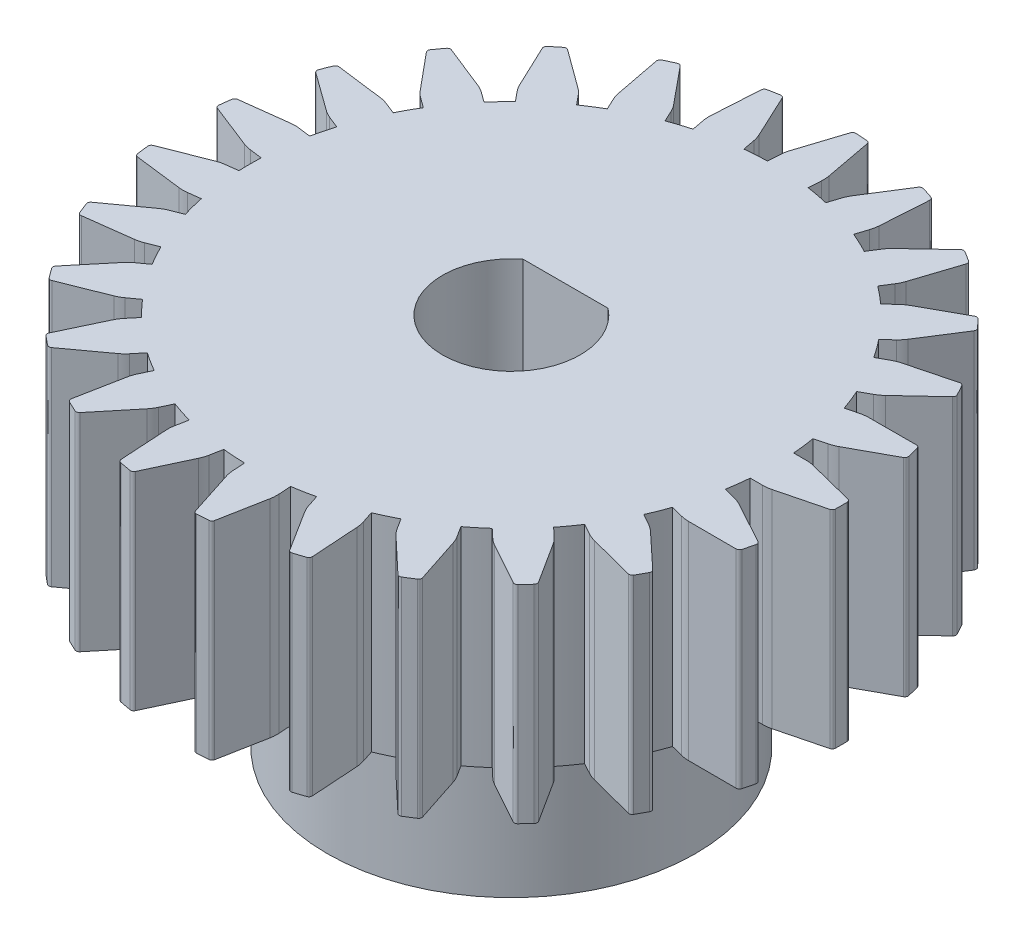
SolidWorks part; units mm, degrees
ref_plane "Front Plane" through (0, 0, 0) normal (0, 0, 1) x (1, 0, 0)
ref_plane "Top Plane" through (0, 0, 0) normal (0, 1, 0) x (1, 0, 0)
ref_plane "Right Plane" through (0, 0, 0) normal (1, 0, 0) x (0, 0, -1)
sketch "Sketch1" plane through (0, 0, 0) normal (0, 1, 0) x (1, 0, 0)
  line L0 (2.0888, 4.0389) -> (-2.9918, 4.0389)
  line L1 (-19.9606, 2.7118) -> (-17.3123, 1.6707)
  line L2 (-16.8313, 1.5479) -> (-16.0874, 1.4539)
  line L3 (-16.0874, 0.124) -> (-16.8313, 0.03)
  line L4 (-17.3123, -0.0928) -> (-19.9606, -1.1339)
  line L5 (-19.8259, -2.2003) -> (-17.0019, -2.5501)
  line L6 (-16.5054, -2.5495) -> (-15.7615, -2.4555)
  line L7 (-15.4308, -3.7436) -> (-16.128, -4.0196)
  line L8 (-16.5633, -4.2583) -> (-18.8695, -5.9252)
  line L9 (-18.4738, -6.9246) -> (-15.6516, -6.5611)
  line L10 (-15.1708, -6.437) -> (-14.4737, -6.161)
  line L11 (-13.833, -7.3264) -> (-14.4396, -7.7671)
  line L12 (-14.802, -8.1065) -> (-16.6211, -10.2946)
  line L13 (-15.9893, -11.1643) -> (-13.3461, -10.1103)
  line L14 (-12.9114, -9.8706) -> (-12.3048, -9.4298)
  line L15 (-11.3944, -10.3993) -> (-11.8724, -10.977)
  line L16 (-12.1389, -11.3959) -> (-13.3568, -13.9676)
  line L17 (-12.5285, -14.6528) -> (-10.2305, -12.9746)
  line L18 (-9.869, -12.6343) -> (-9.3911, -12.0566)
  line L19 (-8.2682, -12.7691) -> (-8.5875, -13.4476)
  line L20 (-8.7415, -13.9196) -> (-9.2815, -16.7134)
  line L21 (-8.3089, -17.1711) -> (-6.5004, -14.9741)
  line L22 (-6.2349, -14.5546) -> (-5.9157, -13.8762)
  line L23 (-4.6509, -14.2871) -> (-4.7914, -15.0237)
  line L24 (-4.8232, -15.5191) -> (-4.6514, -18.3595)
  line L25 (-3.5955, -18.5609) -> (-2.3903, -15.9832)
  line L26 (-2.2374, -15.5109) -> (-2.0969, -14.7743)
  line L27 (-0.7697, -14.8578) -> (-0.7226, -15.6062)
  line L28 (-0.6302, -16.094) -> (0.2425, -18.8024)
  line L29 (1.3153, -18.7349) -> (1.8417, -15.9384)
  line L30 (1.8723, -15.4429) -> (1.8252, -14.6946)
  line L31 (3.1315, -14.4454) -> (3.3632, -15.1585)
  line L32 (3.5741, -15.608) -> (5.0929, -18.0143)
  line L33 (6.1152, -17.6821) -> (5.9296, -14.8426)
  line L34 (5.836, -14.3551) -> (5.6043, -13.6419)
  line L35 (6.8076, -13.0757) -> (7.2093, -13.7088)
  line L36 (7.5253, -14.0917) -> (9.5949, -16.0447)
  line L37 (10.5025, -15.4687) -> (9.6165, -12.7646)
  line L38 (9.4046, -12.3156) -> (9.0028, -11.6825)
  line L39 (10.0275, -10.8348) -> (10.5741, -11.3481)
  line L40 (10.9754, -11.6405) -> (13.4656, -13.0174)
  line L41 (14.2015, -12.2338) -> (12.6709, -9.835)
  line L42 (12.3539, -9.4528) -> (11.8073, -8.9395)
  line L43 (12.589, -7.8636) -> (13.2461, -8.2249)
  line L44 (13.7075, -8.4082) -> (16.4619, -9.1226)
  line L45 (16.9797, -8.1806) -> (14.9007, -6.2378)
  line L46 (14.4986, -5.9465) -> (13.8416, -5.5852)
  line L47 (14.3311, -4.3488) -> (15.0574, -4.5352)
  line L48 (15.5499, -4.5981) -> (18.3954, -4.605)
  line L49 (18.6627, -3.5639) -> (16.1658, -2.1991)
  line L50 (15.704, -2.0169) -> (14.9777, -1.8304)
  line L51 (15.1444, -0.5111) -> (15.8942, -0.5111)
  line L52 (16.3869, -0.4494) -> (19.1447, 0.2515)
  line L53 (19.1447, 1.3264) -> (16.3869, 2.0273)
  line L54 (15.8942, 2.0889) -> (15.1444, 2.0889)
  line L55 (14.9777, 3.4083) -> (15.704, 3.5948)
  line L56 (16.1658, 3.777) -> (18.6627, 5.1418)
  line L57 (18.3954, 6.1829) -> (15.5499, 6.176)
  line L58 (15.0574, 6.1131) -> (14.3311, 5.9267)
  line L59 (13.8416, 7.1631) -> (14.4986, 7.5244)
  line L60 (14.9007, 7.8157) -> (16.9797, 9.7585)
  line L61 (16.4619, 10.7005) -> (13.7075, 9.9861)
  line L62 (13.2461, 9.8028) -> (12.589, 9.4415)
  line L63 (11.8073, 10.5174) -> (12.3539, 11.0307)
  line L64 (12.6709, 11.4129) -> (14.2015, 13.8117)
  line L65 (13.4656, 14.5953) -> (10.9754, 13.2183)
  line L66 (10.5741, 12.926) -> (10.0275, 12.4127)
  line L67 (9.0028, 13.2604) -> (9.4046, 13.8935)
  line L68 (9.6165, 14.3425) -> (10.5025, 17.0466)
  line L69 (9.5949, 17.6226) -> (7.5253, 15.6696)
  line L70 (7.2093, 15.2867) -> (6.8076, 14.6536)
  line L71 (5.6043, 15.2198) -> (5.836, 15.9329)
  line L72 (5.9296, 16.4205) -> (6.1152, 19.26)
  line L73 (5.0929, 19.5922) -> (3.5741, 17.1859)
  line L74 (3.3632, 16.7364) -> (3.1315, 16.0233)
  line L75 (1.8252, 16.2725) -> (1.8723, 17.0208)
  line L76 (1.8417, 17.5163) -> (1.3153, 20.3128)
  line L77 (0.2425, 20.3803) -> (-0.6302, 17.6719)
  line L78 (-0.7226, 17.1841) -> (-0.7697, 16.4357)
  line L79 (-2.0969, 16.3522) -> (-2.2374, 17.0888)
  line L80 (-2.3903, 17.5611) -> (-3.5955, 20.1388)
  line L81 (-4.6514, 19.9374) -> (-4.8232, 17.097)
  line L82 (-4.7914, 16.6016) -> (-4.6509, 15.865)
  line L83 (-5.9157, 15.4541) -> (-6.2349, 16.1325)
  line L84 (-6.5004, 16.552) -> (-8.3089, 18.749)
  line L85 (-9.2815, 18.2913) -> (-8.7415, 15.4975)
  line L86 (-8.5875, 15.0255) -> (-8.2682, 14.347)
  line L87 (-9.3911, 13.6345) -> (-9.869, 14.2122)
  line L88 (-10.2305, 14.5525) -> (-12.5285, 16.2307)
  line L89 (-13.3568, 15.5455) -> (-12.1389, 12.9738)
  line L90 (-11.8724, 12.5549) -> (-11.3944, 11.9772)
  line L91 (-12.3048, 11.0077) -> (-12.9114, 11.4485)
  line L92 (-13.3461, 11.6882) -> (-15.9893, 12.7422)
  line L93 (-16.6211, 11.8725) -> (-14.802, 9.6844)
  line L94 (-14.4396, 9.345) -> (-13.833, 8.9043)
  line L95 (-14.4737, 7.7389) -> (-15.1708, 8.0149)
  line L96 (-15.6516, 8.139) -> (-18.4738, 8.5025)
  line L97 (-18.8695, 7.5031) -> (-16.5633, 5.8362)
  line L98 (-16.128, 5.5975) -> (-15.4308, 5.3215)
  line L99 (-15.7615, 4.0334) -> (-16.5054, 4.1274)
  line L100 (-17.0019, 4.128) -> (-19.8259, 3.7782)
  arc A0 (-2.9918, 4.0389) -> (-4.5765, 0.7889) centre (-0.4515, 0.7889) ccw
  arc A1 (-4.5765, 0.7889) -> (3.6735, 0.7889) centre (-0.4515, 0.7889) ccw
  arc A2 (3.6735, 0.7889) -> (2.0888, 4.0389) centre (-0.4515, 0.7889) ccw
  arc A3 (-19.8259, 3.7782) -> (-19.9992, 3.6083) centre (-19.8013, 3.5798) ccw
  arc A4 (-19.9992, 3.6083) -> (-20.0863, 2.9195) centre (-0.4515, 0.7889) ccw
  arc A5 (-20.0863, 2.9195) -> (-19.9606, 2.7118) centre (-19.8874, 2.8979) ccw
  arc A6 (-17.3123, 1.6707) -> (-16.8313, 1.5479) centre (-16.5806, 3.5321) ccw
  arc A7 (-16.0874, 1.4539) -> (-16.0874, 0.124) centre (-0.4515, 0.7889) ccw
  arc A8 (-16.8313, 0.03) -> (-17.3123, -0.0928) centre (-16.5806, -1.9542) ccw
  arc A9 (-19.9606, -1.1339) -> (-20.0863, -1.3416) centre (-19.8874, -1.32) ccw
  arc A10 (-20.0863, -1.3416) -> (-19.9992, -2.0304) centre (-0.4515, 0.7889) ccw
  arc A11 (-19.9992, -2.0304) -> (-19.8259, -2.2003) centre (-19.8013, -2.0019) ccw
  arc A12 (-17.0019, -2.5501) -> (-16.5054, -2.5495) centre (-16.7561, -0.5652) ccw
  arc A13 (-15.7615, -2.4555) -> (-15.4308, -3.7436) centre (-0.4515, 0.7889) ccw
  arc A14 (-16.128, -4.0196) -> (-16.5633, -4.2583) centre (-15.3917, -5.8792) ccw
  arc A15 (-18.8695, -5.9252) -> (-18.9396, -6.1576) centre (-18.7523, -6.0873) ccw
  arc A16 (-18.9396, -6.1576) -> (-18.684, -6.8032) centre (-0.4515, 0.7889) ccw
  arc A17 (-18.684, -6.8032) -> (-18.4738, -6.9246) centre (-18.4993, -6.7263) ccw
  arc A18 (-15.6516, -6.5611) -> (-15.1708, -6.437) centre (-15.9071, -4.5775) ccw
  arc A19 (-14.4737, -6.161) -> (-13.833, -7.3264) centre (-0.4515, 0.7889) ccw
  arc A20 (-14.4396, -7.7671) -> (-14.802, -8.1065) centre (-13.264, -9.3851) ccw
  arc A21 (-16.6211, -10.2946) -> (-16.6312, -10.5372) centre (-16.4673, -10.4225) ccw
  arc A22 (-16.6312, -10.5372) -> (-16.2231, -11.0989) centre (-0.4515, 0.7889) ccw
  arc A23 (-16.2231, -11.0989) -> (-15.9893, -11.1643) centre (-16.0634, -10.9785) ccw
  arc A24 (-13.3461, -10.1103) -> (-12.9114, -9.8706) centre (-14.0869, -8.2525) ccw
  arc A25 (-12.3048, -9.4298) -> (-11.3944, -10.3993) centre (-0.4515, 0.7889) ccw
  arc A26 (-11.8724, -10.977) -> (-12.1389, -11.3959) centre (-10.3313, -12.2519) ccw
  arc A27 (-13.3568, -13.9676) -> (-13.3062, -14.2051) centre (-13.176, -14.0532) ccw
  arc A28 (-13.3062, -14.2051) -> (-12.7712, -14.6476) centre (-0.4515, 0.7889) ccw
  arc A29 (-12.7712, -14.6476) -> (-12.5285, -14.6528) centre (-12.6465, -14.4913) ccw
  arc A30 (-10.2305, -12.9746) -> (-9.869, -12.6343) centre (-11.41, -11.3595) ccw
  arc A31 (-9.3911, -12.0566) -> (-8.2682, -12.7691) centre (-0.4515, 0.7889) ccw
  arc A32 (-8.5875, -13.4476) -> (-8.7415, -13.9196) centre (-6.7778, -14.2992) ccw
  arc A33 (-9.2815, -16.7134) -> (-9.1735, -16.9308) centre (-9.0851, -16.7514) ccw
  arc A34 (-9.1735, -16.9308) -> (-8.5453, -17.2264) centre (-0.4515, 0.7889) ccw
  arc A35 (-8.5453, -17.2264) -> (-8.3089, -17.1711) centre (-8.4633, -17.044) ccw
  arc A36 (-6.5004, -14.9741) -> (-6.2349, -14.5546) centre (-8.0446, -13.7031) ccw
  arc A37 (-5.9157, -13.8762) -> (-4.6509, -14.2871) centre (-0.4515, 0.7889) ccw
  arc A38 (-4.7914, -15.0237) -> (-4.8232, -15.5191) centre (-2.8268, -15.3984) ccw
  arc A39 (-4.6514, -18.3595) -> (-4.4927, -18.5432) centre (-4.4518, -18.3474) ccw
  arc A40 (-4.4927, -18.5432) -> (-3.8107, -18.6733) centre (-0.4515, 0.7889) ccw
  arc A41 (-3.8107, -18.6733) -> (-3.5955, -18.5609) centre (-3.7767, -18.4762) ccw
  arc A42 (-2.3903, -15.9832) -> (-2.2374, -15.5109) centre (-4.202, -15.1361) ccw
  arc A43 (-2.0969, -14.7743) -> (-0.7697, -14.8578) centre (-0.4515, 0.7889) ccw
  arc A44 (-0.7226, -15.6062) -> (-0.6302, -16.094) centre (1.2735, -15.4806) ccw
  arc A45 (0.2425, -18.8024) -> (0.4419, -18.9408) centre (0.4329, -18.741) ccw
  arc A46 (0.4419, -18.9408) -> (1.1349, -18.8972) centre (-0.4515, 0.7889) ccw
  arc A47 (1.1349, -18.8972) -> (1.3153, -18.7349) centre (1.1188, -18.6979) ccw
  arc A48 (1.8417, -15.9384) -> (1.8723, -15.4429) centre (-0.1238, -15.5685) ccw
  arc A49 (1.8252, -14.6946) -> (3.1315, -14.4454) centre (-0.4515, 0.7889) ccw
  arc A50 (3.3632, -15.1585) -> (3.5741, -15.608) centre (5.2653, -14.5405) ccw
  arc A51 (5.0929, -18.0143) -> (5.3205, -18.0988) centre (5.262, -17.9075) ccw
  arc A52 (5.3205, -18.0988) -> (5.9808, -17.8842) centre (-0.4515, 0.7889) ccw
  arc A53 (5.9808, -17.8842) -> (6.1152, -17.6821) centre (5.9156, -17.6951) ccw
  arc A54 (5.9296, -14.8426) -> (5.836, -14.3551) centre (3.9339, -14.9731) ccw
  arc A55 (5.6043, -13.6419) -> (6.8076, -13.0757) centre (-0.4515, 0.7889) ccw
  arc A56 (7.2093, -13.7088) -> (7.5253, -14.0917) centre (8.898, -12.6371) ccw
  arc A57 (9.5949, -16.0447) -> (9.8363, -16.07) centre (9.7321, -15.8992) ccw
  arc A58 (9.8363, -16.07) -> (10.4225, -15.6979) centre (-0.4515, 0.7889) ccw
  arc A59 (10.4225, -15.6979) -> (10.5025, -15.4687) centre (10.3124, -15.531) ccw
  arc A60 (9.6165, -12.7646) -> (9.4046, -12.3156) centre (7.7159, -13.3873) ccw
  arc A61 (9.0028, -11.6825) -> (10.0275, -10.8348) centre (-0.4515, 0.7889) ccw
  arc A62 (10.5741, -11.3481) -> (10.9754, -11.6405) centre (11.9432, -9.8902) ccw
  arc A63 (13.4656, -13.0174) -> (13.7058, -12.9818) centre (13.5624, -12.8424) ccw
  arc A64 (13.7058, -12.9818) -> (14.181, -12.4757) centre (-0.4515, 0.7889) ccw
  arc A65 (14.181, -12.4757) -> (14.2015, -12.2338) centre (14.0328, -12.3414) ccw
  arc A66 (12.6709, -9.835) -> (12.3539, -9.4528) centre (10.9848, -10.9108) ccw
  arc A67 (11.8073, -8.9395) -> (12.589, -7.8636) centre (-0.4515, 0.7889) ccw
  arc A68 (13.2461, -8.2249) -> (13.7075, -8.4082) centre (14.2096, -6.4723) ccw
  arc A69 (16.4619, -9.1226) -> (16.6856, -9.0284) centre (16.5121, -8.929) ccw
  arc A70 (16.6856, -9.0284) -> (17.0201, -8.42) centre (-0.4515, 0.7889) ccw
  arc A71 (17.0201, -8.42) -> (16.9797, -8.1806) centre (16.8432, -8.3268) ccw
  arc A72 (14.9007, -6.2378) -> (14.4986, -5.9465) centre (13.5351, -7.6991) ccw
  arc A73 (13.8416, -5.5852) -> (14.3311, -4.3488) centre (-0.4515, 0.7889) ccw
  arc A74 (15.0574, -4.5352) -> (15.5499, -4.5981) centre (15.5548, -2.5981) ccw
  arc A75 (18.3954, -4.605) -> (18.5887, -4.4582) centre (18.3959, -4.405) ccw
  arc A76 (18.5887, -4.4582) -> (18.7614, -3.7857) centre (-0.4515, 0.7889) ccw
  arc A77 (18.7614, -3.7857) -> (18.6627, -3.5639) centre (18.5668, -3.7394) ccw
  arc A78 (16.1658, -2.1991) -> (15.704, -2.0169) centre (15.2066, -3.9541) ccw
  arc A79 (14.9777, -1.8304) -> (15.1444, -0.5111) centre (-0.4515, 0.7889) ccw
  arc A80 (15.8942, -0.5111) -> (16.3869, -0.4494) centre (15.8942, 1.4889) ccw
  arc A81 (19.1447, 0.2515) -> (19.2954, 0.4418) centre (19.0955, 0.4453) ccw
  arc A82 (19.2954, 0.4418) -> (19.2954, 1.1361) centre (-0.4515, 0.7889) ccw
  arc A83 (19.2954, 1.1361) -> (19.1447, 1.3264) centre (19.0955, 1.1326) ccw
  arc A84 (16.3869, 2.0273) -> (15.8942, 2.0889) centre (15.8942, 0.0889) ccw
  arc A85 (15.1444, 2.0889) -> (14.9777, 3.4083) centre (-0.4515, 0.7889) ccw
  arc A86 (15.704, 3.5948) -> (16.1658, 3.777) centre (15.2066, 5.532) ccw
  arc A87 (18.6627, 5.1418) -> (18.7614, 5.3636) centre (18.5668, 5.3172) ccw
  arc A88 (18.7614, 5.3636) -> (18.5887, 6.0361) centre (-0.4515, 0.7889) ccw
  arc A89 (18.5887, 6.0361) -> (18.3954, 6.1829) centre (18.3959, 5.9829) ccw
  arc A90 (15.5499, 6.176) -> (15.0574, 6.1131) centre (15.5548, 4.176) ccw
  arc A91 (14.3311, 5.9267) -> (13.8416, 7.1631) centre (-0.4515, 0.7889) ccw
  arc A92 (14.4986, 7.5244) -> (14.9007, 7.8157) centre (13.5351, 9.277) ccw
  arc A93 (16.9797, 9.7585) -> (17.0201, 9.9979) centre (16.8432, 9.9047) ccw
  arc A94 (17.0201, 9.9979) -> (16.6856, 10.6063) centre (-0.4515, 0.7889) ccw
  arc A95 (16.6856, 10.6063) -> (16.4619, 10.7005) centre (16.5121, 10.5069) ccw
  arc A96 (13.7075, 9.9861) -> (13.2461, 9.8028) centre (14.2096, 8.0502) ccw
  arc A97 (12.589, 9.4415) -> (11.8073, 10.5174) centre (-0.4515, 0.7889) ccw
  arc A98 (12.3539, 11.0307) -> (12.6709, 11.4129) centre (10.9848, 12.4887) ccw
  arc A99 (14.2015, 13.8117) -> (14.181, 14.0536) centre (14.0328, 13.9193) ccw
  arc A100 (14.181, 14.0536) -> (13.7058, 14.5597) centre (-0.4515, 0.7889) ccw
  arc A101 (13.7058, 14.5597) -> (13.4656, 14.5953) centre (13.5624, 14.4203) ccw
  arc A102 (10.9754, 13.2183) -> (10.5741, 12.926) centre (11.9432, 11.4681) ccw
  arc A103 (10.0275, 12.4127) -> (9.0028, 13.2604) centre (-0.4515, 0.7889) ccw
  arc A104 (9.4046, 13.8935) -> (9.6165, 14.3425) centre (7.7159, 14.9652) ccw
  arc A105 (10.5025, 17.0466) -> (10.4225, 17.2758) centre (10.3124, 17.1089) ccw
  arc A106 (10.4225, 17.2758) -> (9.8363, 17.6479) centre (-0.4515, 0.7889) ccw
  arc A107 (9.8363, 17.6479) -> (9.5949, 17.6226) centre (9.7321, 17.4771) ccw
  arc A108 (7.5253, 15.6696) -> (7.2093, 15.2867) centre (8.898, 14.215) ccw
  arc A109 (6.8076, 14.6536) -> (5.6043, 15.2198) centre (-0.4515, 0.7889) ccw
  arc A110 (5.836, 15.9329) -> (5.9296, 16.4205) centre (3.9339, 16.551) ccw
  arc A111 (6.1152, 19.26) -> (5.9808, 19.4621) centre (5.9156, 19.273) ccw
  arc A112 (5.9808, 19.4621) -> (5.3205, 19.6767) centre (-0.4515, 0.7889) ccw
  arc A113 (5.3205, 19.6767) -> (5.0929, 19.5922) centre (5.262, 19.4854) ccw
  arc A114 (3.5741, 17.1859) -> (3.3632, 16.7364) centre (5.2653, 16.1184) ccw
  arc A115 (3.1315, 16.0233) -> (1.8252, 16.2725) centre (-0.4515, 0.7889) ccw
  arc A116 (1.8723, 17.0208) -> (1.8417, 17.5163) centre (-0.1238, 17.1464) ccw
  arc A117 (1.3153, 20.3128) -> (1.1349, 20.4751) centre (1.1188, 20.2758) ccw
  arc A118 (1.1349, 20.4751) -> (0.4419, 20.5187) centre (-0.4515, 0.7889) ccw
  arc A119 (0.4419, 20.5187) -> (0.2425, 20.3803) centre (0.4329, 20.3189) ccw
  arc A120 (-0.6302, 17.6719) -> (-0.7226, 17.1841) centre (1.2735, 17.0585) ccw
  arc A121 (-0.7697, 16.4357) -> (-2.0969, 16.3522) centre (-0.4515, 0.7889) ccw
  arc A122 (-2.2374, 17.0888) -> (-2.3903, 17.5611) centre (-4.202, 16.714) ccw
  arc A123 (-3.5955, 20.1388) -> (-3.8107, 20.2512) centre (-3.7767, 20.0541) ccw
  arc A124 (-3.8107, 20.2512) -> (-4.4927, 20.1211) centre (-0.4515, 0.7889) ccw
  arc A125 (-4.4927, 20.1211) -> (-4.6514, 19.9374) centre (-4.4518, 19.9253) ccw
  arc A126 (-4.8232, 17.097) -> (-4.7914, 16.6016) centre (-2.8268, 16.9763) ccw
  arc A127 (-4.6509, 15.865) -> (-5.9157, 15.4541) centre (-0.4515, 0.7889) ccw
  arc A128 (-6.2349, 16.1325) -> (-6.5004, 16.552) centre (-8.0446, 15.281) ccw
  arc A129 (-8.3089, 18.749) -> (-8.5453, 18.8043) centre (-8.4633, 18.6219) ccw
  arc A130 (-8.5453, 18.8043) -> (-9.1735, 18.5087) centre (-0.4515, 0.7889) ccw
  arc A131 (-9.1735, 18.5087) -> (-9.2815, 18.2913) centre (-9.0851, 18.3293) ccw
  arc A132 (-8.7415, 15.4975) -> (-8.5875, 15.0255) centre (-6.7778, 15.8771) ccw
  arc A133 (-8.2682, 14.347) -> (-9.3911, 13.6345) centre (-0.4515, 0.7889) ccw
  arc A134 (-9.869, 14.2122) -> (-10.2305, 14.5525) centre (-11.41, 12.9374) ccw
  arc A135 (-12.5285, 16.2307) -> (-12.7712, 16.2255) centre (-12.6465, 16.0692) ccw
  arc A136 (-12.7712, 16.2255) -> (-13.3062, 15.783) centre (-0.4515, 0.7889) ccw
  arc A137 (-13.3062, 15.783) -> (-13.3568, 15.5455) centre (-13.176, 15.6311) ccw
  arc A138 (-12.1389, 12.9738) -> (-11.8724, 12.5549) centre (-10.3313, 13.8298) ccw
  arc A139 (-11.3944, 11.9772) -> (-12.3048, 11.0077) centre (-0.4515, 0.7889) ccw
  arc A140 (-12.9114, 11.4485) -> (-13.3461, 11.6882) centre (-14.0869, 9.8304) ccw
  arc A141 (-15.9893, 12.7422) -> (-16.2231, 12.6768) centre (-16.0634, 12.5564) ccw
  arc A142 (-16.2231, 12.6768) -> (-16.6312, 12.1151) centre (-0.4515, 0.7889) ccw
  arc A143 (-16.6312, 12.1151) -> (-16.6211, 11.8725) centre (-16.4673, 12.0004) ccw
  arc A144 (-14.802, 9.6844) -> (-14.4396, 9.345) centre (-13.264, 10.963) ccw
  arc A145 (-13.833, 8.9043) -> (-14.4737, 7.7389) centre (-0.4515, 0.7889) ccw
  arc A146 (-15.1708, 8.0149) -> (-15.6516, 8.139) centre (-15.9071, 6.1554) ccw
  arc A147 (-18.4738, 8.5025) -> (-18.684, 8.3811) centre (-18.4993, 8.3042) ccw
  arc A148 (-18.684, 8.3811) -> (-18.9396, 7.7355) centre (-0.4515, 0.7889) ccw
  arc A149 (-18.9396, 7.7355) -> (-18.8695, 7.5031) centre (-18.7523, 7.6652) ccw
  arc A150 (-16.5633, 5.8362) -> (-16.128, 5.5975) centre (-15.3917, 7.4571) ccw
  arc A151 (-15.4308, 5.3215) -> (-15.7615, 4.0334) centre (-0.4515, 0.7889) ccw
  arc A152 (-16.5054, 4.1274) -> (-17.0019, 4.128) centre (-16.7561, 2.1431) ccw
extrude "Boss-Extrude1" add sketch "Sketch1" along normal blind 12.4
sketch "Sketch2" plane through (0, 0, 0) normal (0, -1, 0) x (1, 0, 0)
  line L0 (2.0888, -4.0389) -> (-2.9918, -4.0389) construction
  line L1 (2.0888, -4.0389) -> (-2.9918, -4.0389)
  line L2 (4.071, -12.0389) -> (-4.974, -12.0389)
  arc A0 (2.0888, -4.0389) -> (-2.9918, -4.0389) centre (-0.4515, -0.7889) ccw construction
  arc A1 (2.0888, -4.0389) -> (-2.9918, -4.0389) centre (-0.4515, -0.7889) ccw
  arc A2 (4.071, -12.0389) -> (-4.974, -12.0389) centre (-0.4515, -0.7889) ccw
  dimension "D1" = 8
extrude "Boss-Extrude2" add sketch "Sketch2" along normal blind 10
sketch "Sketch3" plane through (0, 0, -12.0389) normal (0, 0, -1) x (-1, 0, 0)
  line L0 (-4.071, -10) -> (4.974, 0) construction
  circle A0 centre (0.4515, -5) radius 1
  dimension "D2" = 2
extrude "Cut-Extrude1" cut sketch "Sketch3" against normal blind 10
sketch "Sketch6" plane through (0, -10, 0) normal (0, -1, 0) x (1, 0, 0)
  line L0 (-4.5637, -11.0183) -> (3.6607, -11.0183)
  line L1 (-4.974, -12.0389) -> (4.071, -12.0389)
  line L2 (-4.974, -12.0389) -> (4.071, -12.0389)
  arc A1 (4.071, -12.0389) -> (-4.974, -12.0389) centre (-0.4515, -0.7889) ccw
  arc A2 (4.071, -12.0389) -> (-4.974, -12.0389) centre (-0.4515, -0.7889) ccw
  arc A3 (3.6607, -11.0183) -> (-4.5637, -11.0183) centre (-0.4515, -0.7889) ccw
  dimension "D1" = 0
  dimension "D3" = 1.1
extrude "Cut-Extrude2" cut sketch "Sketch6" against normal blind 10
